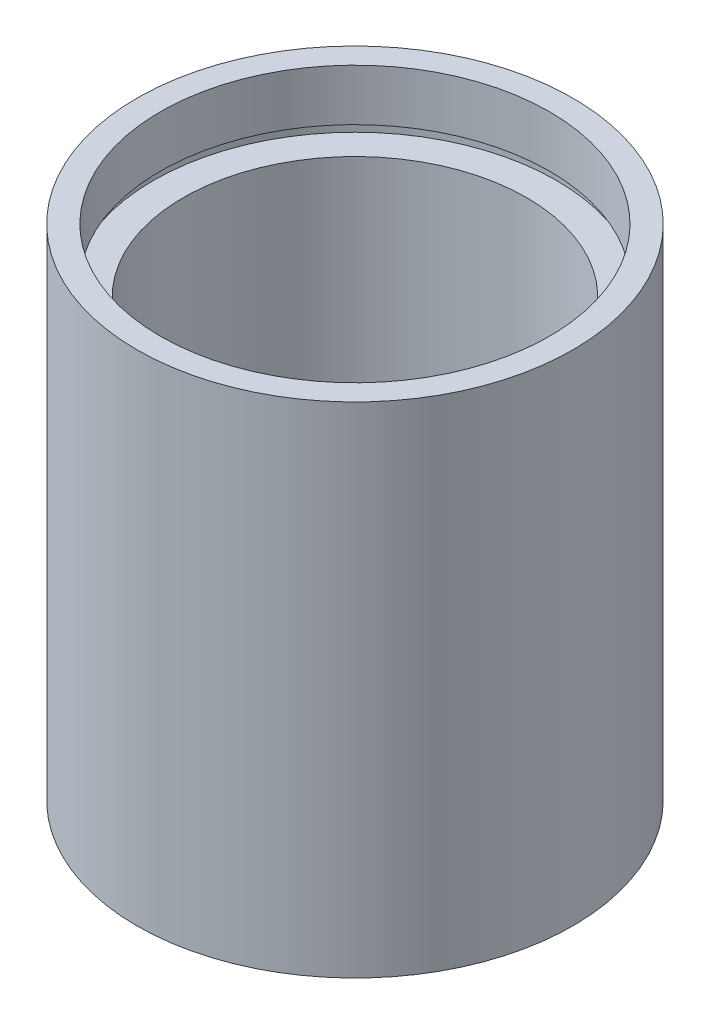
SolidWorks part; units mm, degrees
ref_plane "前视基准面" through (0, 0, 0) normal (0, 0, 1) x (1, 0, 0)
ref_plane "上视基准面" through (0, 0, 0) normal (0, 1, 0) x (1, 0, 0)
ref_plane "右视基准面" through (0, 0, 0) normal (1, 0, 0) x (0, 0, -1)
sketch "草图1" plane through (0, 0, 0) normal (0, 0, 1) x (1, 0, 0)
  line L0 (0, 161.3762) -> (0, 0) construction
  line L1 (141.7365, 0) -> (-131.7984, 0) construction
  line L2 (19.05, 0) -> (19.05, 43.6)
  line L3 (17, 0) -> (17, 4.5)
  line L4 (17.6, 4.5) -> (17.6, 5.5)
  line L5 (15, 5.5) -> (15, 38.1)
  line L6 (15, 5.5) -> (17.6, 5.5)
  line L7 (17.6, 38.1) -> (17.6, 39.1)
  line L8 (15, 38.1) -> (17.6, 38.1)
  line L9 (17, 39.1) -> (17, 43.6)
  line L10 (17.6, 39.1) -> (17, 39.1)
  line L11 (17, 43.6) -> (19.05, 43.6)
  line L12 (17, 0) -> (19.05, 0)
  line L13 (17, 4.5) -> (17.6, 4.5)
  dimension "D1" = 19.05
  dimension "D2" = 17
  dimension "D3" = 4.5
  dimension "D4" = 17.6
  dimension "D5" = 15
  dimension "D6" = 17.6
  dimension "D7" = 1
  dimension "D8" = 5.5
  dimension "D9" = 38.1
  dimension "D10" = 17
  dimension "D11" = 1
revolve "旋转1" add sketch "草图1" angle 360 about L0
cosmetic thread "装饰螺纹线1" parameters "D2"=35
cosmetic thread "装饰螺纹线2" parameters "D2"=31
cosmetic thread "装饰螺纹线3" parameters "D2"=35
